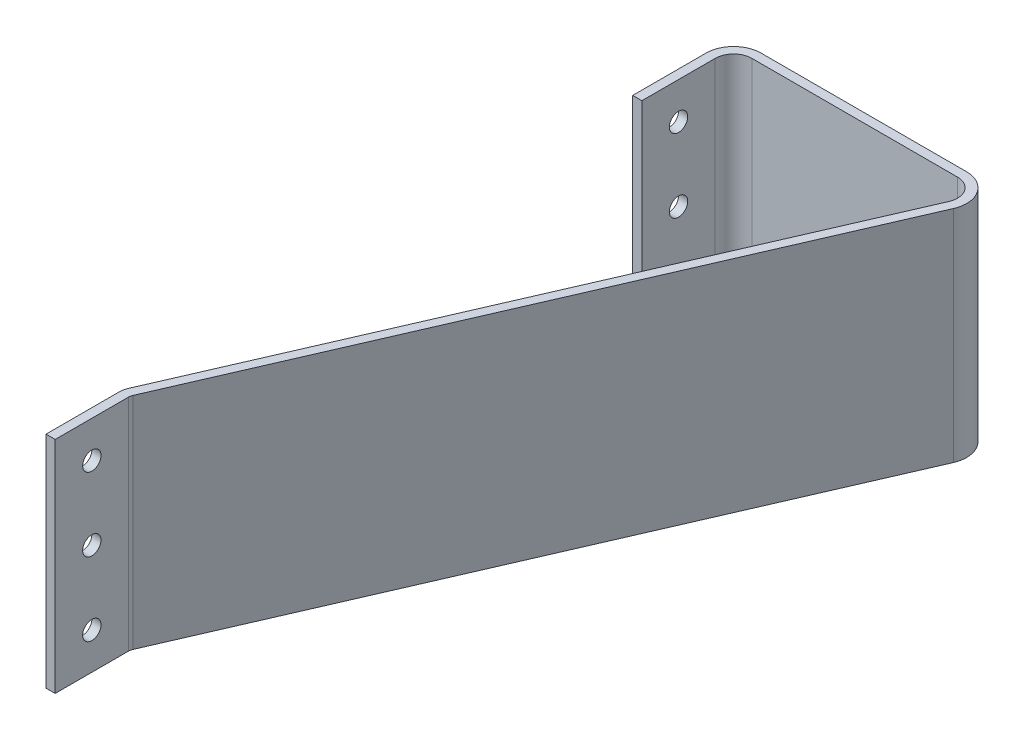
SolidWorks part; units mm, degrees
material "Acrylic (Medium-high impact)"
ref_plane "Front Plane" through (0, 0, 0) normal (0, 0, 1) x (1, 0, 0)
ref_plane "Top Plane" through (0, 0, 0) normal (0, 1, 0) x (1, 0, 0)
ref_plane "Right Plane" through (0, 0, 0) normal (1, 0, 0) x (0, 0, -1)
sketch "Sketch1" plane through (0, 0, 0) normal (0, 1, 0) x (1, 0, 0)
  line L0 (-279.4, 0) -> (279.4, 0) construction
  line L1 (0, 0) -> (0, 50000) construction
  line L2 (-184.15, 238.125) -> (184.15, 238.125) construction
  line L3 (-279.4, 0) -> (-279.4, 25.4)
  line L4 (-278.8747, 27.929) -> (-192.845, 226.071)
  line L5 (-198.6696, 234.95) -> (-269.875, 234.95)
  line L6 (-276.225, 0) -> (-276.225, 25.4)
  line L7 (-275.9623, 26.6645) -> (-189.9326, 224.8065)
  line L9 (-184.15, 238.125) -> (-189.9326, 224.8065) construction
  line L11 (-279.4, 12.7) -> (-276.225, 12.7) construction
  line L12 (-279.4, 0) -> (-276.225, 0)
  line L13 (-277.8125, 236.5375) -> (-186.5699, 236.5375) construction
  line L14 (-186.5699, 236.5375) -> (-277.8125, 26.3893) construction
  line L15 (-277.8125, 26.3893) -> (-277.8125, 0) construction
  line L16 (-192.845, 226.071) -> (-189.9326, 224.8065) construction
  line L17 (-278.8747, 27.929) -> (-275.9623, 26.6645) construction
  line L18 (-198.6696, 234.95) -> (-276.2351, 234.95) construction
  line L19 (-276.225, 228.6) -> (-276.225, 203.2)
  line L20 (-269.875, 238.125) -> (-198.6696, 238.125)
  line L21 (-198.6696, 238.125) -> (-276.2351, 238.125) construction
  line L22 (-269.875, 238.125) -> (-269.875, 234.95) construction
  line L23 (-198.6696, 238.125) -> (-198.6696, 234.95) construction
  line L24 (-276.225, 215.9) -> (-279.4, 215.9) construction
  line L27 (-279.4, 228.6) -> (-279.4, 203.2)
  line L28 (-279.4, 203.2) -> (-276.225, 203.2)
  line L29 (-277.8125, 203.2) -> (-277.8125, 236.5375) construction
  arc A0 (-192.845, 226.071) -> (-198.6696, 234.95) centre (-198.6696, 228.6) ccw
  arc A1 (-279.4, 25.4) -> (-278.8747, 27.929) centre (-273.05, 25.4) cw
  arc A2 (-276.225, 25.4) -> (-275.9623, 26.6645) centre (-273.05, 25.4) cw
  arc A3 (-189.9326, 224.8065) -> (-198.6696, 238.125) centre (-198.6696, 228.6) ccw
  arc A4 (-276.225, 228.6) -> (-269.875, 234.95) centre (-269.875, 228.6) cw
  arc A9 (-279.4, 228.6) -> (-269.875, 238.125) centre (-269.875, 228.6) cw
  point P4 (0, 0)
  point P10 (0, 238.125)
  point P31 (-191.3888, 225.4388)
  point P33 (-277.4185, 27.2967)
  point P39 (-278.4176, 28.7929)
  point P40 (-269.875, 236.5375)
  dimension "D3" = 6.35
  dimension "D5" = 6.35
  dimension "D1" = 558.8
  dimension "D2" = 368.3
  dimension "D6" = 25.4
  dimension "D7" = 25.4
  dimension "D8" = 203.2
  dimension "D9" = 3.175
  dimension "D4" = 3.175
extrude "Boss-Extrude1" add sketch "Sketch1" along normal blind 76.2
sketch "Sketch2" plane through (-276.225, 0, 0) normal (1, 0, 0) x (0, 0, -1)
  line L0 (12.7, 76.2) -> (12.7, 0) construction
  line L1 (0, 76.2) -> (25.4, 76.2) construction
  line L2 (0, 0) -> (25.4, 0) construction
  circle A0 centre (12.7, 63.5) radius 3.175
  circle A2 centre (12.7, 12.7) radius 3.175
  circle A3 centre (12.7, 38.1) radius 3.175
  dimension "D1" = 6.35
  dimension "D2" = 25.4
  dimension "D3" = 25.4
extrude "Cut-Extrude1" cut sketch "Sketch2" against normal through all both and the other way through all
sketch "Sketch4" plane through (-279.4, 0, 0) normal (-1, 0, 0) x (0, 0, 1)
  line L0 (-215.9, 76.2) -> (-215.9, 0) construction
  line L1 (-228.6, 76.2) -> (-203.2, 76.2) construction
  line L2 (-228.6, 0) -> (-203.2, 0) construction
  circle A0 centre (-215.9, 38.1) radius 3.175
  circle A1 centre (-215.9, 63.5) radius 3.175
  circle A2 centre (-215.9, 12.7) radius 3.175
  dimension "D1" = 6.35
  dimension "D2" = 25.4
  dimension "D3" = 25.4
extrude "Cut-Extrude3" cut sketch "Sketch4" against normal up to surface (3.175 mm away) up to face at (-276.225, 38.1, -215.9)
